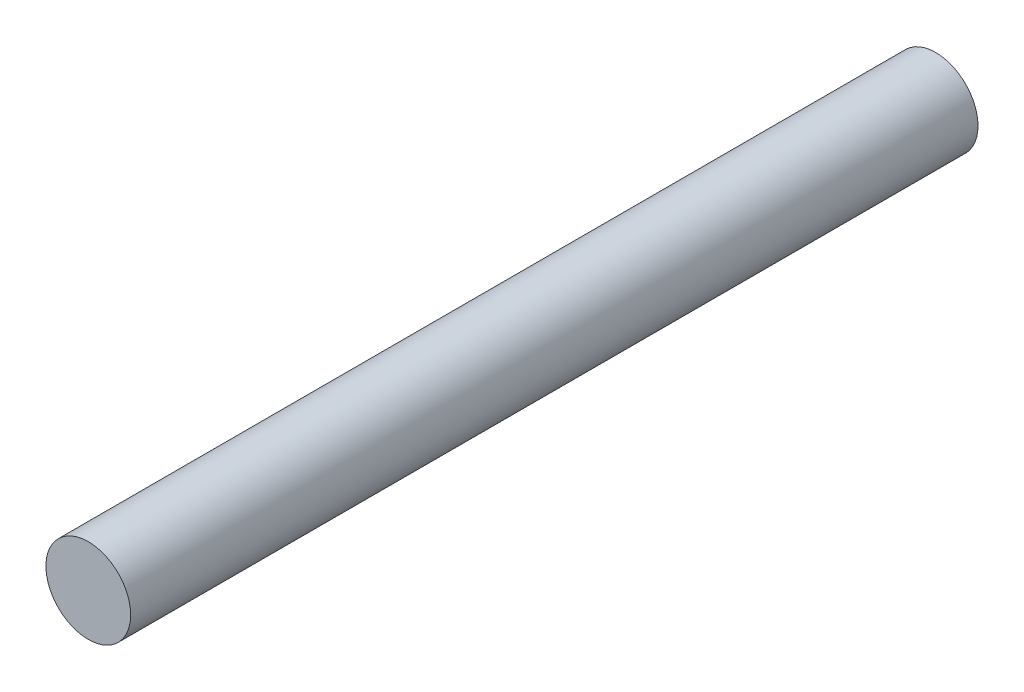
SolidWorks part; units mm, degrees
ref_plane "Front Plane" through (0, 0, 0) normal (0, 0, 1) x (1, 0, 0)
ref_plane "Top Plane" through (0, 0, 0) normal (0, 1, 0) x (1, 0, 0)
ref_plane "Right Plane" through (0, 0, 0) normal (1, 0, 0) x (0, 0, -1)
sketch "Sketch1" plane through (0, 0, 0) normal (0, 0, 1) x (1, 0, 0)
  circle A0 centre (0, 0) radius 4
  dimension "D1" = 8
extrude "Boss-Extrude1" add sketch "Sketch1" along normal blind 80
